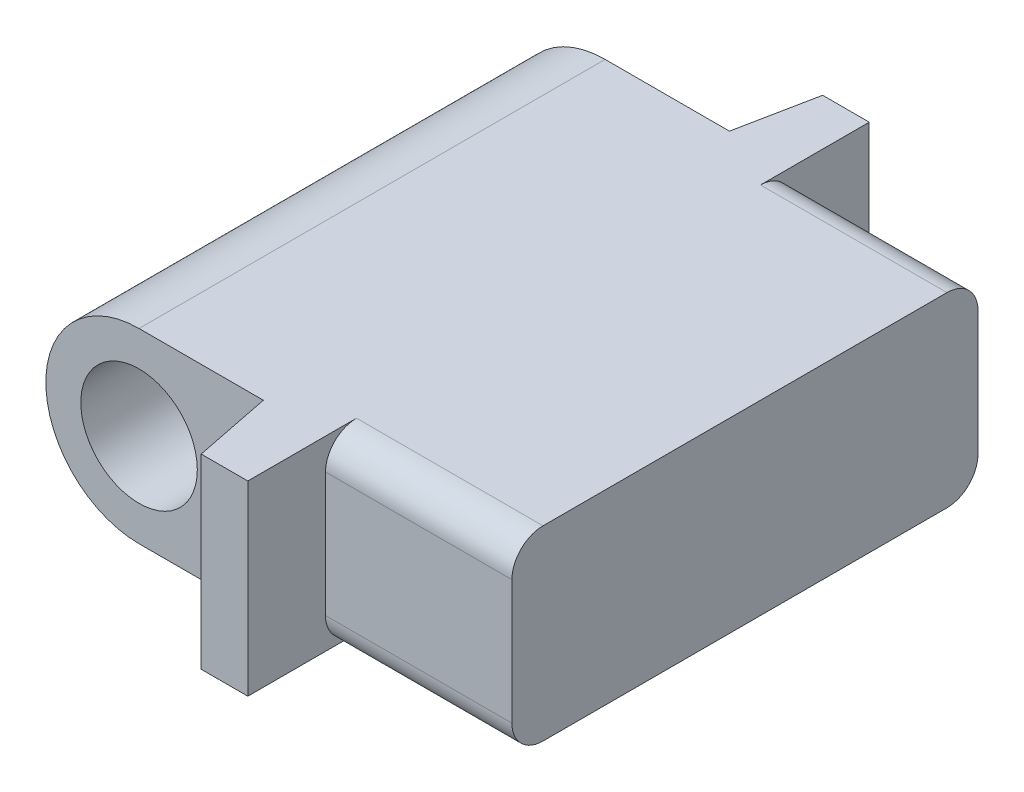
SolidWorks part; units mm, degrees
material "PTFE (general)"
ref_plane "Front Plane" through (0, 0, 0) normal (0, 0, 1) x (1, 0, 0)
ref_plane "Top Plane" through (0, 0, 0) normal (0, 1, 0) x (1, 0, 0)
ref_plane "Right Plane" through (0, 0, 0) normal (1, 0, 0) x (0, 0, -1)
sketch "Sketch1" plane through (0, 0, 0) normal (0, 1, 0) x (1, 0, 0)
  line L1 (19.05, -25.4) -> (-19.05, -25.4)
  line L2 (19.05, -25.4) -> (19.05, 25.4)
  line L3 (19.05, 25.4) -> (-19.05, 25.4)
  line L4 (-19.05, -25.4) -> (-19.05, 25.4)
  line L5 (19.05, -25.4) -> (-19.05, 25.4) construction
  line L6 (19.05, 25.4) -> (-19.05, -25.4) construction
  point P0 (0, 0)
  dimension "D1" = 38.1
  dimension "D2" = 50.8
extrude "Boss-Extrude1" add sketch "Sketch1" along normal blind 15.24
sketch "Sketch2" plane through (0, 15.24, 0) normal (0, 1, 0) x (1, 0, 0)
  line L0 (-19.05, 0) -> (19.05, 0) construction
  line L1 (-19.05, 25.4) -> (-1.27, 25.4)
  line L2 (-19.05, 25.4) -> (-19.05, 19.05)
  line L3 (-19.05, 19.05) -> (-1.27, 19.05)
  line L4 (-1.27, 25.4) -> (-1.27, 19.05)
  line L5 (-19.05, 25.4) -> (-19.05, -25.4) construction
  line L6 (19.05, -25.4) -> (19.05, 25.4) construction
  line L7 (-1.27, 19.05) -> (0, 25.4)
  line L8 (19.05, 25.4) -> (-19.05, 25.4) construction
  line L9 (0, 25.4) -> (3.81, 25.4)
  line L10 (3.81, 25.4) -> (3.81, 19.05)
  line L11 (3.81, 19.05) -> (19.05, 19.05)
  line L12 (3.81, -19.05) -> (19.05, -19.05)
  line L13 (3.81, -25.4) -> (3.81, -19.05)
  line L14 (0, -25.4) -> (3.81, -25.4)
  line L15 (-1.27, -19.05) -> (0, -25.4)
  line L16 (-1.27, -25.4) -> (-1.27, -19.05)
  line L17 (-19.05, -19.05) -> (-1.27, -19.05)
  line L18 (-19.05, -25.4) -> (-19.05, -19.05)
  line L19 (-19.05, -25.4) -> (-1.27, -25.4)
  line M7 (-19.05, 25.4) -> (-19.05, -25.4)
  line M8 (-19.05, -25.4) -> (19.05, -25.4)
  line M9 (19.05, -25.4) -> (19.05, 25.4)
  line M10 (19.05, 25.4) -> (-19.05, 25.4)
  dimension "D1" = 17.78
  dimension "D2" = 6.35
  dimension "D3" = 3.81
  dimension "D4" = 5.08
extrude "Cut-Extrude1" cut sketch "Sketch2" against normal blind 15.24 contours L4 L3 M10 M7 | L10 L11 M9 M10 | L17 L16 M7 M8 | L13 L12 M8 M9 | L16 L15 M8 | L4 L7 M10
sketch "Sketch3" plane through (0, 0, 19.05) normal (0, 0, 1) x (1, 0, 0)
  line L0 (-19.05, 0) -> (-19.05, 15.24) construction
  line L1 (-19.05, 0) -> (-1.27, 0) construction
  line L2 (-19.05, 15.24) -> (-1.27, 15.24) construction
  line L3 (-11.43, 15.24) -> (-19.05, 15.24)
  line L4 (-19.05, 15.24) -> (-19.05, 0)
  line L5 (-19.05, 0) -> (-11.43, 0)
  circle A0 centre (-11.43, 7.62) radius 7.62
  circle A1 centre (-11.43, 7.62) radius 4.7625
  line M1 (-1.27, 15.24) -> (-19.05, 15.24)
  line M2 (-19.05, 15.24) -> (-19.05, 0)
  line M3 (-19.05, 0) -> (-1.27, 0)
  dimension "D1" = 9.525
extrude "Cut-Extrude2" cut sketch "Sketch3" against normal through all contours A0 M1 M2 | A0 L4 M3 | A1
fillet "Fillet1" radius 2.54 4 edges at (11.43, 15.24, -19.05) (11.43, 0, -19.05) (11.43, 0, 19.05) (11.43, 15.24, 19.05)
